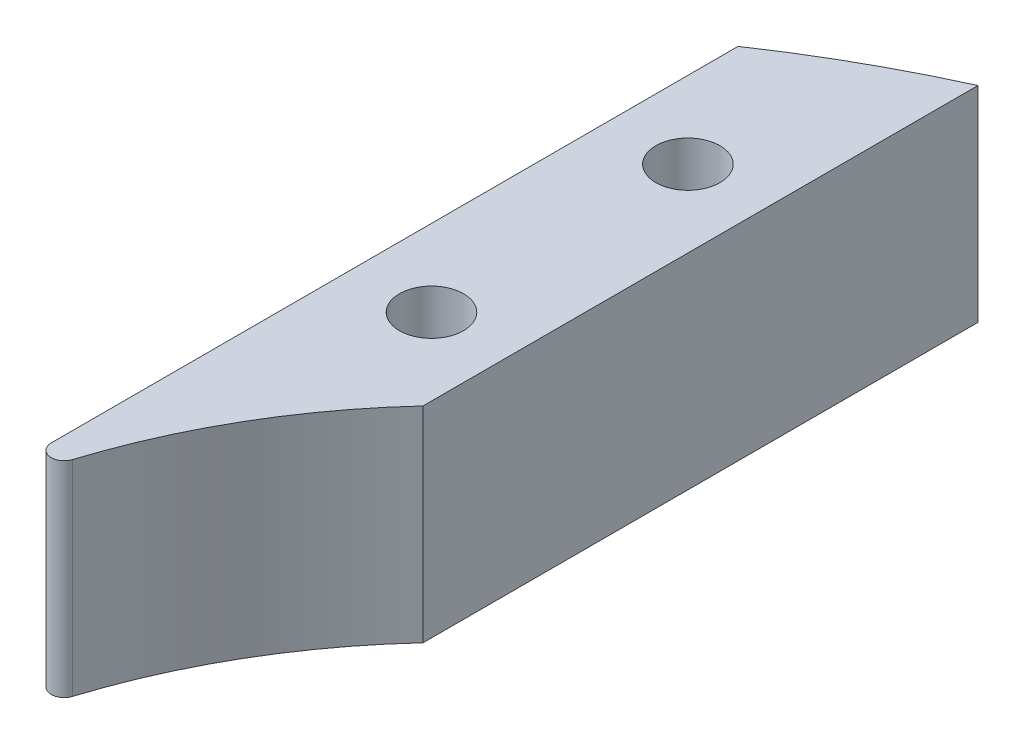
SolidWorks part; units mm, degrees
material "6061 合金"
ref_plane "前视基准面" through (0, 0, 0) normal (0, 0, 1) x (1, 0, 0)
ref_plane "上视基准面" through (0, 0, 0) normal (0, 1, 0) x (1, 0, 0)
ref_plane "右视基准面" through (0, 0, 0) normal (1, 0, 0) x (0, 0, -1)
sketch "草图1" plane through (0, 0, 0) normal (0, 1, 0) x (1, 0, 0)
  line L0 (-46.9, 0) -> (-46.9, 46.9)
  line L1 (-46.9, 46.9) -> (-16.9, 46.9)
  line L2 (-16.9, 46.9) -> (-16.9, 46.5747)
  line L3 (-31.9, 0) -> (-31.9, 46.9) construction
  line L4 (-19.9, 46.9) -> (-19.9, 39.1306) construction
  line L5 (-19.9, 46.9) -> (-19.9, 43.7493) construction
  line L6 (-43.9, 0) -> (-43.9, 46.9) construction
  line L7 (-16.9, 46.9) -> (-16.9, 43.7493) construction
  line L8 (-22.9, 2.1424) -> (-22.9, 46.9) construction
  line L9 (-19.9, 39.1306) -> (-19.9, 18.9319) construction
  line L10 (-22.9, 33.8881) -> (-22.9, 2.1424)
  line L11 (-16.9, 37.2451) -> (-16.9, 15.601)
  arc A0 (-46.9, 0) -> (-14.2906, 44.6698) centre (0, 0) ccw
  circle A1 centre (0, 0) radius 40.9 construction
  circle A2 centre (0, 0) radius 31.9 construction
  circle A3 centre (0, 0) radius 22.9 construction
  circle A4 centre (0, 0) radius 43.9 construction
  circle A5 centre (-19.9, 39.1306) radius 1.25
  circle A6 centre (0, 43.9) radius 1.25
  circle A7 centre (43.9, 0) radius 1.25
  circle A8 centre (0, -43.9) radius 1.25
  circle A9 centre (-43.9, 0) radius 1.25
  circle A10 centre (0, 0) radius 17.025
  circle A11 centre (0, 0) radius 19 construction
  circle A12 centre (0, 19) radius 1.525
  circle A13 centre (13.435, 13.435) radius 1.525
  circle A14 centre (19, 0) radius 1.525
  circle A15 centre (13.435, -13.435) radius 1.525
  circle A16 centre (0, -19) radius 1.525
  circle A17 centre (-13.435, -13.435) radius 1.525
  circle A18 centre (-19, 0) radius 1.525
  circle A19 centre (-13.435, 13.435) radius 1.525
  circle A20 centre (0, 0) radius 46.9 construction
  circle A21 centre (-43.9, 39.1306) radius 1.25
  arc A22 (-16.9, 46.5747) -> (-14.2906, 44.6698) centre (-14.9, 46.5747) ccw
  circle A23 centre (-19.9, 28.9319) radius 1.25
  circle A24 centre (-19.9, 18.9319) radius 1.25
  arc A25 (-22.9, 33.8881) -> (-16.9, 37.2451) centre (0, 0) cw
  arc A26 (-22.9, 2.1424) -> (-16.9, 15.601) centre (0, 0) cw
  point P58 (-19.9, 24.9319)
  dimension "D1" = 93.8
  dimension "D8" = 2.5
  dimension "D9" = 34.05
  dimension "D10" = 38
  dimension "D11" = 3.05
  dimension "D13" = 2
  dimension "D14" = 4
  dimension "D16" = 23
  dimension "D15" = 6
  dimension "D2" = 6
  dimension "D3" = 9
  dimension "D4" = 9
  dimension "D5" = 3
  dimension "D6" = 3
  dimension "D7" = 4
  dimension "D12" = 8
extrude "凸台-拉伸1" add sketch "草图1" along normal blind 8 contours L10 A26 L11 A25 A23 A24
cosmetic thread "装饰螺纹线1" parameters "D2"=3
cosmetic thread "装饰螺纹线2" parameters "D2"=3
fillet "圆角1" radius 0.5 1 edges at (-22.9, 4, -2.1424)
